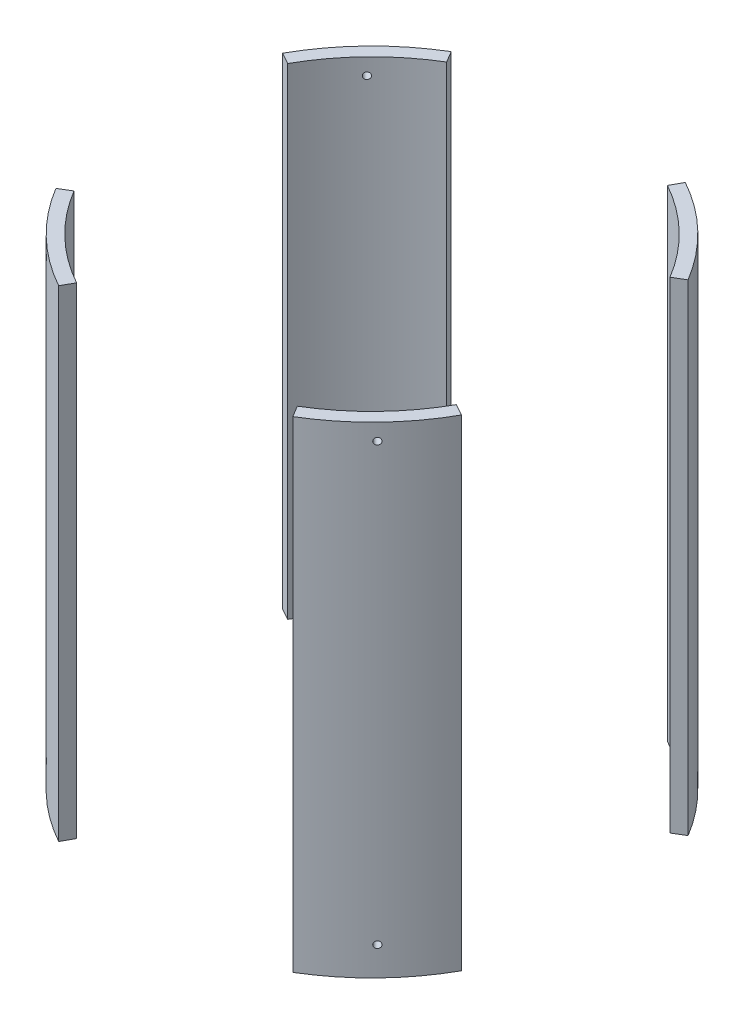
SolidWorks part; units mm, degrees
material "6061-T6 (SS)"
ref_plane "Front Plane" through (0, 0, 0) normal (0, 0, 1) x (1, 0, 0)
ref_plane "Top Plane" through (0, 0, 0) normal (0, 1, 0) x (1, 0, 0)
ref_plane "Right Plane" through (0, 0, 0) normal (1, 0, 0) x (0, 0, -1)
sketch "Sketch2" plane through (0, 0, 0) normal (0, 1, 0) x (1, 0, 0)
  circle A0 centre (0, 0) radius 88.9
  circle A1 centre (0, 0) radius 83.82
  dimension "D1" = 177.8
  dimension "D2" = 167.64
extrude "Boss-Extrude1" add sketch "Sketch2" along normal mid plane 185.7245
sketch "Sketch3" plane through (0, 0, 0) normal (0, 1, 0) x (1, 0, 0)
  line L0 (0, 0) -> (169.6618, 101.6776)
  line L1 (-58.1167, 96.9749) -> (0, 0)
  line L2 (0, 0) -> (53.9, 96.9749)
  line L3 (53.9, 96.9749) -> (-58.1167, 96.9749)
  line L4 (0, 0) -> (70.9917, -118.4586)
  line L5 (70.9917, -118.4586) -> (-65.8409, -118.4586)
  line L6 (-65.8409, -118.4586) -> (0, 0)
  line L7 (169.6618, 101.6776) -> (169.6618, -94.3004)
  line L8 (169.6618, -94.3004) -> (0, 0)
  line L9 (0, 0) -> (-123.7413, 68.7771)
  line L10 (-123.7413, 68.7771) -> (-123.7413, -74.1577)
  line L11 (-123.7413, -74.1577) -> (0, 0)
  dimension "D1" = 60
  dimension "D2" = 60
  dimension "D3" = 60
  dimension "D4" = 60
  dimension "D5" = 30
  dimension "D6" = 30
extrude "Cut-Extrude1" cut sketch "Sketch3" against normal through all both and the other way through all contours L8 L7 L0 | L2 L3 L1 | L10 L11 L9 | L6 L5 L4
ref_plane "Bolt reference plane" through (-56.3092, 0, 58.1758) normal (0.6955, 0, -0.7185) x (-0.7185, 0, -0.6955)
sketch "Sketch5" plane through (-56.3092, 0, 58.1758) normal (0.6955, 0, -0.7185) x (-0.7185, 0, -0.6955)
  line L0 (-23.009, -92.8623) -> (23.009, -92.8623) construction
  circle A0 centre (-0.0228, 86.5123) radius 1.27
  circle A1 centre (-0.0228, -81.7498) radius 1.27
  dimension "D1" = 2.54
  dimension "D4" = 11.1125
  dimension "D2" = 21.717
  dimension "D3" = 6.35
extrude "Bolt holes" cut sketch "Sketch5" against normal through all
pattern_circular "Bolt pattern" count 4 over 360 about axis through (0, 92.8623, 0) along (0, 1, 0) of "Bolt holes"
equation "\"D1@Boss-Extrude1\"=3*12"
